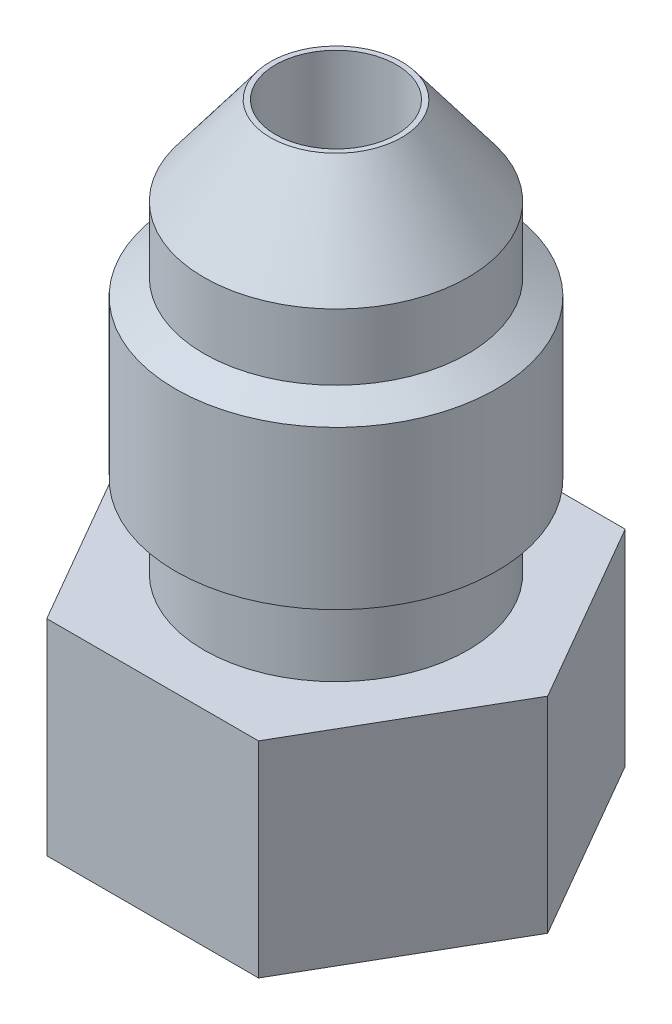
SolidWorks part; units mm, degrees
material "Plain Carbon Steel"
ref_plane "Front Plane" through (0, 0, 0) normal (0, 0, 1) x (1, 0, 0)
ref_plane "Top Plane" through (0, 0, 0) normal (0, 1, 0) x (1, 0, 0)
ref_plane "Right Plane" through (0, 0, 0) normal (1, 0, 0) x (0, 0, -1)
sketch "Sketch1" plane through (0, 0, 0) normal (0, 1, 0) x (1, 0, 0)
  line L1 (7.3323, 0) -> (3.6662, 6.35)
  line L2 (3.6662, 6.35) -> (-3.6662, 6.35)
  line L3 (-3.6662, 6.35) -> (-7.3323, 0)
  line L4 (-7.3323, 0) -> (-3.6662, -6.35)
  line L5 (-3.6662, -6.35) -> (3.6662, -6.35)
  line L6 (3.6662, -6.35) -> (7.3323, 0)
  circle A0 centre (0, 0) radius 6.35 construction
  dimension "D1" = 12.7
extrude "Boss-Extrude1" add sketch "Sketch1" along normal blind 7.112
sketch "Sketch2" plane through (0, 7.112, 0) normal (0, 1, 0) x (1, 0, 0)
  circle A0 centre (0, 0) radius 4.572
  dimension "D1" = 9.144
extrude "Boss-Extrude2" add sketch "Sketch2" along normal blind 11.176
sketch "Sketch3" plane through (0, 0, 0) normal (0, 0, 1) x (1, 0, 0)
  line L0 (0, 24.8544) -> (0, 16.886) construction
  line L1 (0, 18.288) -> (-4.572, 18.288)
  line L2 (4.572, 18.288) -> (-4.572, 18.288) construction
  line L3 (-4.572, 18.288) -> (-2.2752, 21.336)
  line L4 (-2.2752, 21.336) -> (0, 21.336)
  line L5 (-4.572, 18.288) -> (-4.572, 7.112) construction
  line L6 (0, 18.288) -> (0, 21.336)
  dimension "D1" = 37
  dimension "D2" = 3.048
revolve "Revolve1" add sketch "Sketch3" angle 360 about L0
sketch "Sketch4" plane through (0, 0, 0) normal (0, -1, 0) x (1, 0, 0)
  circle A0 centre (0, 0) radius 4.0005
  dimension "D1" = 8.001
extrude "Cut-Extrude1" cut sketch "Sketch4" against normal blind 4.7625
sketch "Sketch5" plane through (0, 21.336, 0) normal (0, 1, 0) x (1, 0, 0)
  circle A0 centre (0, 0) radius 2.0955
  dimension "D1" = 4.191
extrude "Cut-Extrude2" cut sketch "Sketch5" against normal through all
sketch "Sketch7" plane through (0, 0, 0) normal (0, 0, 1) x (1, 0, 0)
  line L0 (0, 22.3816) -> (0, 5.3624) construction
  line L1 (-4.572, 9.398) -> (-5.5562, 9.9663)
  line L2 (-4.572, 18.288) -> (-4.572, 7.112) construction
  line L3 (-5.5562, 9.9663) -> (-5.5562, 15.4337)
  line L4 (-5.5562, 15.4337) -> (-4.572, 16.002)
  line L5 (-4.572, 16.002) -> (-4.572, 9.398)
  line L6 (-7.3323, 7.112) -> (-3.6662, 7.112) construction
  dimension "D1" = 5.5562
  dimension "D2" = 2.286
  dimension "D3" = 2.286
  dimension "D4" = 60
revolve "Revolve2" add sketch "Sketch7" angle 360 about L0
